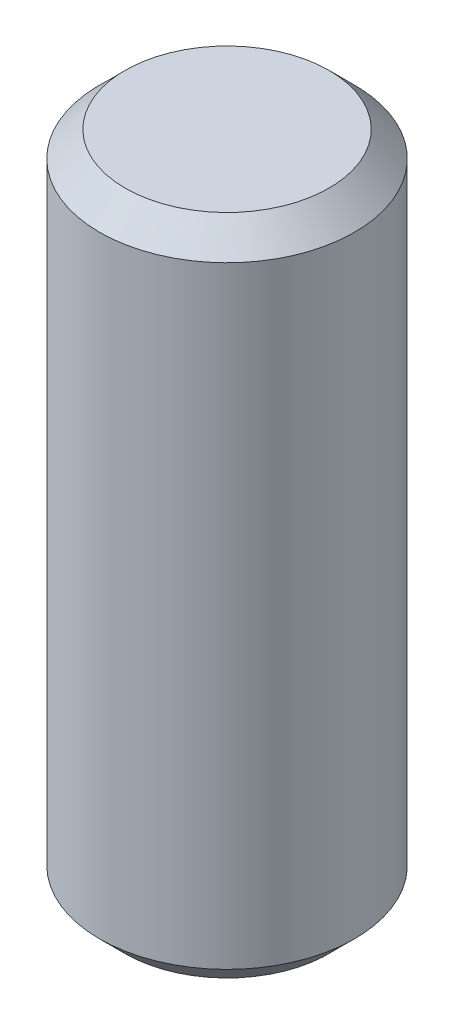
SolidWorks part; units mm, degrees
material "AISI 304"
ref_plane "Front Plane" through (0, 0, 0) normal (0, 0, 1) x (1, 0, 0)
ref_plane "Top Plane" through (0, 0, 0) normal (0, 1, 0) x (1, 0, 0)
ref_plane "Right Plane" through (0, 0, 0) normal (1, 0, 0) x (0, 0, -1)
sketch "Sketch1" plane through (0, 0, 0) normal (0, 1, 0) x (1, 0, 0)
  circle A0 centre (0, 0) radius 10
  dimension "D1" = 20
extrude "Boss-Extrude1" add sketch "Sketch1" along normal blind 52 contours A0
chamfer "Chamfer1" distance 2 angle 45 2 edges at (0, 52, 10) (0, 0, 10)
